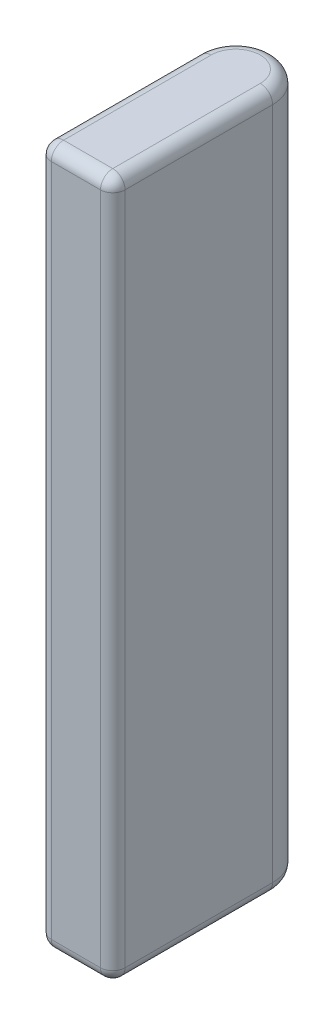
SolidWorks part; units mm, degrees
ref_plane "前视基准面" through (0, 0, 0) normal (0, 0, 1) x (1, 0, 0)
ref_plane "上视基准面" through (0, 0, 0) normal (0, 1, 0) x (1, 0, 0)
ref_plane "右视基准面" through (0, 0, 0) normal (1, 0, 0) x (0, 0, -1)
other "Configuration Table"
sketch "草图1" plane through (0, 0, 0) normal (0, 1, 0) x (1, 0, 0)
  line L1 (-1.5, 3.25) -> (1.5, 3.25)
  line L2 (-1.5, 3.25) -> (-1.5, -3.25)
  line L3 (-1.5, -3.25) -> (1.5, -3.25)
  line L4 (1.5, 3.25) -> (1.5, -3.25)
  line L5 (-1.5, 3.25) -> (1.5, -3.25) construction
  line L6 (-1.5, -3.25) -> (1.5, 3.25) construction
  circle A0 centre (0, 3.25) radius 1.5
  point P0 (0, 0)
  dimension "D1" = 3
  dimension "D2" = 6.5
extrude "凸台-拉伸1" add sketch "草图1" along normal blind 28.4 contours L1 A0 | L1 A0 | A0 L2 L3 L4
fillet "圆角1" radius 0.5 10 edges at (-1.5, 14.2, 3.25) (1.5, 14.2, 3.25) (-1.5, 0, 0) (-1.5, 28.4, 0) (0, 0, 3.25) (0, 28.4, 3.25) (1.5, 0, 0) (1.5, 28.4, 0) (0, 0, -4.75) (0, 28.4, -4.75)
